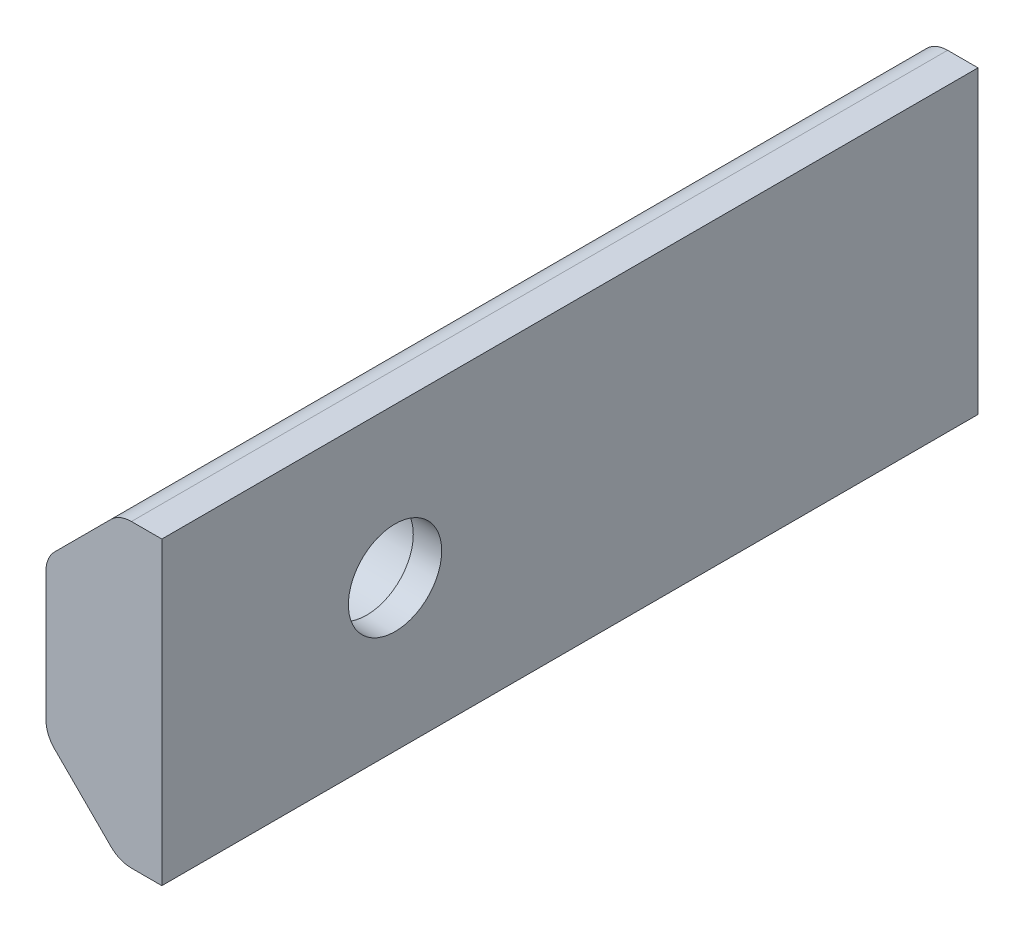
SolidWorks part; units mm, degrees
ref_plane "Front Plane" through (0, 0, 0) normal (0, 0, 1) x (1, 0, 0)
ref_plane "Top Plane" through (0, 0, 0) normal (0, 1, 0) x (1, 0, 0)
ref_plane "Right Plane" through (0, 0, 0) normal (1, 0, 0) x (0, 0, -1)
sketch "Sketch1" plane through (0, 0, 0) normal (0, 0, 1) x (1, 0, 0)
  line L0 (1.9338, 5.15) -> (1.9338, -5.15)
  line L1 (1.9338, -5.15) -> (0.4765, -5.15)
  line L2 (0.4765, -5.15) -> (-2.0404, -2.6331)
  line L3 (-2.0404, -2.6331) -> (-2.0404, 2.6331)
  line L4 (-2.0404, 2.6331) -> (0.4765, 5.15)
  line L5 (0.4765, 5.15) -> (1.9338, 5.15)
  line L6 (1.9338, 0) -> (0, 0) construction
  line L7 (0, 0) -> (-2.0404, 0) construction
  line L8 (0.4765, 5.15) -> (0.4765, -5.15) construction
  dimension "D1" = 10.3
  dimension "D2" = 5.2663
extrude "Boss-Extrude1" add sketch "Sketch1" along normal blind 36
sketch "Sketch2" plane through (1.9338, 0, 0) normal (1, 0, 0) x (0, 0, -1)
  line L0 (-36, 0) -> (-31, 0) construction
  line L1 (-31, 0) -> (-20, 0) construction
  line L2 (-20, 0) -> (-20, 5.15) construction
  line L3 (-36, 5.15) -> (0, 5.15) construction
  line L4 (-36, -5.15) -> (-36, 5.15) construction
  line L6 (-20, 0) -> (0, 0) construction
  circle A0 centre (-20, 0) radius 1.6
  circle A1 centre (-31, 0) radius 1.6
  dimension "D1" = 3.2
  dimension "D2" = 5
  dimension "D3" = 5.15
  dimension "D4" = 11
extrude "Cut-Extrude1" cut sketch "Sketch2" against normal blind 10
sketch "Sketch3" plane through (-2.0404, 0, 0) normal (-1, 0, 0) x (0, 0, 1)
  circle A0 centre (20, 0) radius 1.95
  circle A1 centre (31, 0) radius 1.95
  dimension "D1" = 3.9
extrude "Cut-Extrude2" cut sketch "Sketch3" against normal blind 3
fillet "Fillet1" radius 1 4 edges at (0.4765, -5.15, 18) (-2.0404, -2.6331, 18) (-2.0404, 2.6331, 18) (0.4765, 5.15, 18)
sketch "Sketch4" plane through (1.9338, 0, 0) normal (1, 0, 0) x (0, 0, -1)
  line L0 (-36, -5.15) -> (0, -5.15) construction
  line L1 (-36, 5.15) -> (-28, 5.15)
  line L2 (-36, 5.15) -> (-36, -5.15)
  line L3 (-36, -5.15) -> (-28, -5.15)
  line L4 (-28, 5.15) -> (-28, -5.15)
  dimension "D1" = 8
extrude "Cut-Extrude3" cut sketch "Sketch4" against normal blind 10
